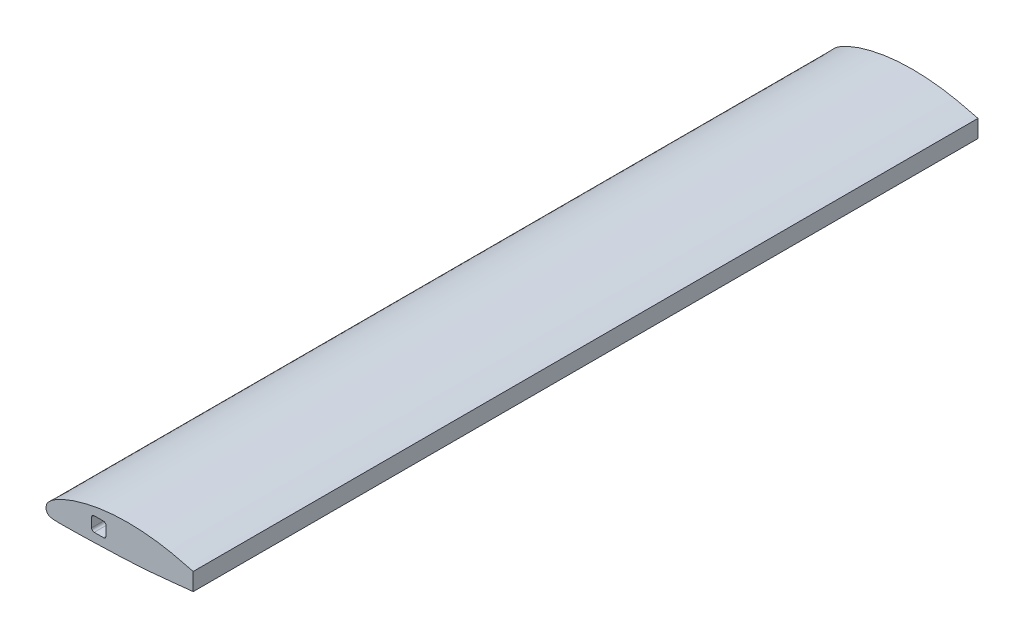
SolidWorks part; units mm, degrees
material "Wing Foam"
ref_plane "Front Plane" through (0, 0, 0) normal (0, 0, 1) x (1, 0, 0)
ref_plane "Top Plane" through (0, 0, 0) normal (0, 1, 0) x (1, 0, 0)
ref_plane "Right Plane" through (0, 0, 0) normal (1, 0, 0) x (0, 0, -1)
curve "Curve1"
  spline degree 3 poles (25.2073, 0.0831, 0) (25.4867, -0.0413, 0) (25.2065, 0.1018, 0) (25.0451, 0.1488, 0) (24.7905, 0.2354, 0) (24.512, 0.3191, 0) (24.1862, 0.415, 0) (23.8224, 0.5184, 0) (23.4192, 0.6311, 0) (22.9787, 0.7524, 0) (22.5024, 0.8828, 0) (21.992, 1.0218, 0) (21.4492, 1.1695, 0) (20.8759, 1.3256, 0) (20.2741, 1.4891, 0) (19.6466, 1.6619, 0) (18.9917, 1.8333, 0) (18.325, 2.0421, 0) (17.625, 2.2014, 0) (16.918, 2.3933, 0) (16.1932, 2.5703, 0) (15.4566, 2.7375, 0) (14.7104, 2.8879, 0) (13.9573, 3.0202, 0) (13.2001, 3.1321, 0) (12.4415, 3.2228, 0) (11.684, 3.2913, 0) (10.9305, 3.3367, 0) (10.1835, 3.3587, 0) (9.4457, 3.3585, 0) (8.7197, 3.336, 0) (8.0081, 3.2917, 0) (7.3132, 3.2267, 0) (6.6377, 3.1395, 0) (5.9841, 3.0331, 0) (5.3544, 2.9102, 0) (4.7508, 2.7729, 0) (4.1756, 2.6228, 0) (3.6307, 2.4616, 0) (3.118, 2.2911, 0) (2.6394, 2.1129, 0) (2.1964, 1.9285, 0) (1.7907, 1.7399, 0) (1.4236, 1.5487, 0) (1.0964, 1.3566, 0) (0.8101, 1.1655, 0) (0.5655, 0.9766, 0) (0.3618, 0.7902, 0) (0.2027, 0.6023, 0) (0.0715, 0.3961, 0) (0.0291, 0.1867, 0) (-0.0105, -0.0161, 0) (0.0146, -0.202, 0) (0.0835, -0.3893, 0) (0.1957, -0.5546, 0) (0.3573, -0.6861, 0) (0.5679, -0.7631, 0) (0.8154, -0.8005, 0) (1.1017, -0.8208, 0) (1.4284, -0.8311, 0) (1.795, -0.8378, 0) (2.2003, -0.8263, 0) (2.6429, -0.8333, 0) (3.1212, -0.8225, 0) (3.6335, -0.8137, 0) (4.1782, -0.8014, 0) (4.7531, -0.7878, 0) (5.3564, -0.7722, 0) (5.9859, -0.755, 0) (6.6394, -0.7358, 0) (7.3145, -0.7145, 0) (8.009, -0.6907, 0) (8.7203, -0.6638, 0) (9.446, -0.6335, 0) (10.1835, -0.5982, 0) (10.9302, -0.5555, 0) (11.6834, -0.5048, 0) (12.4406, -0.4465, 0) (13.199, -0.3808, 0) (13.956, -0.3084, 0) (14.7088, -0.2307, 0) (15.4548, -0.1506, 0) (16.1915, -0.0718, 0) (16.9163, 0.0037, 0) (17.6266, 0.0743, 0) (18.32, 0.1387, 0) (18.9939, 0.1957, 0) (19.646, 0.2444, 0) (20.274, 0.2839, 0) (20.8758, 0.3139, 0) (21.4491, 0.3334, 0) (21.9919, 0.3444, 0) (22.5024, 0.3431, 0) (22.9788, 0.3338, 0) (23.4193, 0.3149, 0) (23.8226, 0.2877, 0) (24.1865, 0.2533, 0) (24.5121, 0.2115, 0) (24.791, 0.1687, 0) (25.0447, 0.1113, 0) (25.2073, 0.0831, 0) (25.4867, -0.0413, 0) (25.2065, 0.1018, 0) knots -0.011667 -0.007006 -0.003134 0 0.003263 0.007251 0.012052 0.017662 0.024068 0.03125 0.039185 0.047848 0.057211 0.067242 0.077909 0.089174 0.100999 0.113341 0.126157 0.139462 0.153011 0.166928 0.181082 0.195404 0.209838 0.224333 0.238842 0.253325 0.26774 0.282049 0.296213 0.310196 0.323962 0.337476 0.350702 0.363611 0.376164 0.388326 0.400059 0.411327 0.422098 0.432339 0.44202 0.451113 0.459592 0.467435 0.474622 0.48114 0.486983 0.492171 0.496782 0.50097 0.505872 0.508789 0.51267 0.516326 0.52007 0.52388 0.527961 0.532642 0.538069 0.544264 0.551215 0.5589 0.567291 0.576362 0.58608 0.596409 0.607315 0.618758 0.630699 0.643095 0.655904 0.669079 0.682577 0.696348 0.710348 0.724529 0.738844 0.753243 0.767678 0.782097 0.796449 0.810678 0.824729 0.838548 0.852084 0.865288 0.878112 0.890511 0.902443 0.913866 0.924742 0.935036 0.944714 0.953747 0.962106 0.969765 0.976703 0.982899 0.988333 0.992994 0.996866 1 1.003263 1.007251 1.012052 periodic
sketch "Sketch4" plane through (0, 0, 0) normal (0, 0, 1) x (1, 0, 0)
  line L0 (292.1, 79.5958) -> (292.1, -43.6108) construction
  line L1 (292.1, 36.0891) -> (292.1, 1.334)
  line L2 (113.919, 33.5909) -> (95.631, 33.5909)
  line L3 (118.999, 28.5109) -> (118.999, 10.2229)
  line L4 (90.551, 28.5109) -> (90.551, 10.2229)
  line L5 (113.919, 5.1429) -> (95.631, 5.1429)
  line L6 (104.775, 51.0135) -> (104.775, -12.2796) construction
  arc A0 (118.999, 10.2229) -> (113.919, 5.1429) centre (113.919, 10.2229) cw
  arc A1 (90.551, 10.2229) -> (95.631, 5.1429) centre (95.631, 10.2229) ccw
  arc A2 (95.631, 33.5909) -> (90.551, 28.5109) centre (95.631, 28.5109) ccw
  arc A3 (118.999, 28.5109) -> (113.919, 33.5909) centre (113.919, 28.5109) ccw
  spline S1 degree 3 poles (415.9211, 1.3711) (420.5305, -0.682) (415.908, 1.6802) (413.2438, 2.4545) (409.0433, 3.884) (404.4481, 5.2647) (399.073, 6.8467) (393.0699, 8.5538) (386.4165, 10.4126) (379.1493, 12.4152) (371.2904, 14.5663) (362.8676, 16.8601) (353.9113, 19.2971) (344.4532, 21.873) (334.5234, 24.5699) (324.1693, 27.4216) (313.3627, 30.2499) (302.3629, 33.6946) (290.8121, 36.3225) (279.1478, 39.4898) (267.187, 42.4092) (255.0347, 45.1684) (242.7212, 47.6502) (230.2962, 49.8339) (217.8019, 51.68) (205.284, 53.1757) (192.7863, 54.3071) (180.3525, 55.0552) (168.027, 55.419) (155.8537, 55.4157) (143.8748, 55.0432) (132.1329, 54.3129) (120.6671, 53.2411) (109.5226, 51.8022) (98.7372, 50.0463) (88.3471, 48.019) (78.3889, 45.7523) (68.8976, 43.2761) (59.9068, 40.617) (51.4478, 37.8028) (43.5499, 34.862) (36.2413, 31.8209) (29.5472, 28.7079) (23.49, 25.5532) (18.0912, 22.3841) (13.3659, 19.2305) (9.3303, 16.1138) (5.9699, 13.039) (3.3452, 9.9386) (1.1802, 6.5357) (0.4796, 3.0799) (-0.1731, -0.2662) (0.2403, -3.3329) (1.3782, -6.4238) (3.2292, -9.1502) (5.896, -11.3207) (9.3708, -12.5914) (13.4534, -13.2083) (18.1779, -13.5437) (23.5691, -13.7123) (29.6183, -13.8232) (36.3042, -13.6335) (43.6074, -13.7495) (51.4991, -13.5705) (59.9532, -13.4254) (68.9395, -13.2237) (78.4265, -12.9982) (88.3809, -12.7417) (98.7674, -12.457) (109.5495, -12.1405) (120.6893, -11.7888) (132.1478, -11.3961) (143.8845, -10.9535) (155.8583, -10.4528) (168.0272, -9.87) (180.3479, -9.1658) (192.7765, -8.329) (205.27, -7.3671) (217.7837, -6.2836) (230.2734, -5.0881) (242.6944, -3.8057) (255.0037, -2.4847) (267.1595, -1.1839) (279.1189, 0.0609) (290.8394, 1.2255) (302.2794, 2.2893) (313.399, 3.2292) (324.1588, 4.0332) (334.5214, 4.6846) (344.4499, 5.1792) (353.9095, 5.5015) (362.8665, 5.6826) (371.2899, 5.6614) (379.15, 5.5073) (386.418, 5.1955) (393.0723, 4.7466) (399.0768, 4.1795) (404.4505, 3.49) (409.0513, 2.784) (413.237, 1.837) (415.9211, 1.3711) (420.5305, -0.682) (415.908, 1.6802) knots -0.011667 -0.007006 -0.003134 0 0.003263 0.007251 0.012052 0.017662 0.024068 0.03125 0.039185 0.047848 0.057211 0.067242 0.077909 0.089174 0.100999 0.113341 0.126157 0.139462 0.153011 0.166928 0.181082 0.195404 0.209838 0.224333 0.238842 0.253325 0.26774 0.282049 0.296213 0.310196 0.323962 0.337476 0.350702 0.363611 0.376164 0.388326 0.400059 0.411327 0.422098 0.432339 0.44202 0.451113 0.459592 0.467435 0.474622 0.48114 0.486983 0.492171 0.496782 0.50097 0.505872 0.508789 0.51267 0.516326 0.52007 0.52388 0.527961 0.532642 0.538069 0.544264 0.551215 0.5589 0.567291 0.576362 0.58608 0.596409 0.607315 0.618758 0.630699 0.643095 0.655904 0.669079 0.682577 0.696348 0.710348 0.724529 0.738844 0.753243 0.767678 0.782097 0.796449 0.810678 0.824729 0.838548 0.852084 0.865288 0.878112 0.890511 0.902443 0.913866 0.924742 0.935036 0.944714 0.953747 0.962106 0.969765 0.976703 0.982899 0.988333 0.992994 0.996866 1 1.003263 1.007251 1.012052 only from (419.1, 0) to (419.1, 0)
  point P14 (90.551, 5.1429)
  point P17 (90.551, 33.5909)
  point P20 (118.999, 33.5909)
  point P21 (104.775, 19.3669)
  point P29 (104.775, 33.5909)
  point P30 (104.775, 5.1429)
  point P31 (118.999, 19.3669)
  point P32 (90.551, 19.3669)
  dimension "D5" = 5.08
  dimension "D1" = 419.1
  dimension "D2" = 127
  dimension "D3" = 28.448
  dimension "D4" = 28.448
  dimension "D6" = 104.775
extrude "Boss-Extrude2" add sketch "Sketch4" along normal blind 1557.3248 contours L1 S1
ref_plane "CG (5.5\")" through (139.7, 0, 0) normal (1, 0, 0) x (0, 0, -1)
sketch "CG_5.5\"" plane through (0, 0, 1557.3248) normal (0, 0, 1) x (1, 0, 0)
  point P0 (139.7, 0)
  point P1 (0, 0)
  dimension "D1" = 139.7
equation "\"AR\"= 7.5"
equation "\"Chord\"= 16.5"
equation "\"D1@Sketch4\"=\"Chord\""
equation "\"D1@Boss-Extrude2\"=\"AR\"*\"Chord\"*0.5 - (1.126/2)"
equation "\"D6@Sketch4\"=\"Chord\"/4"
